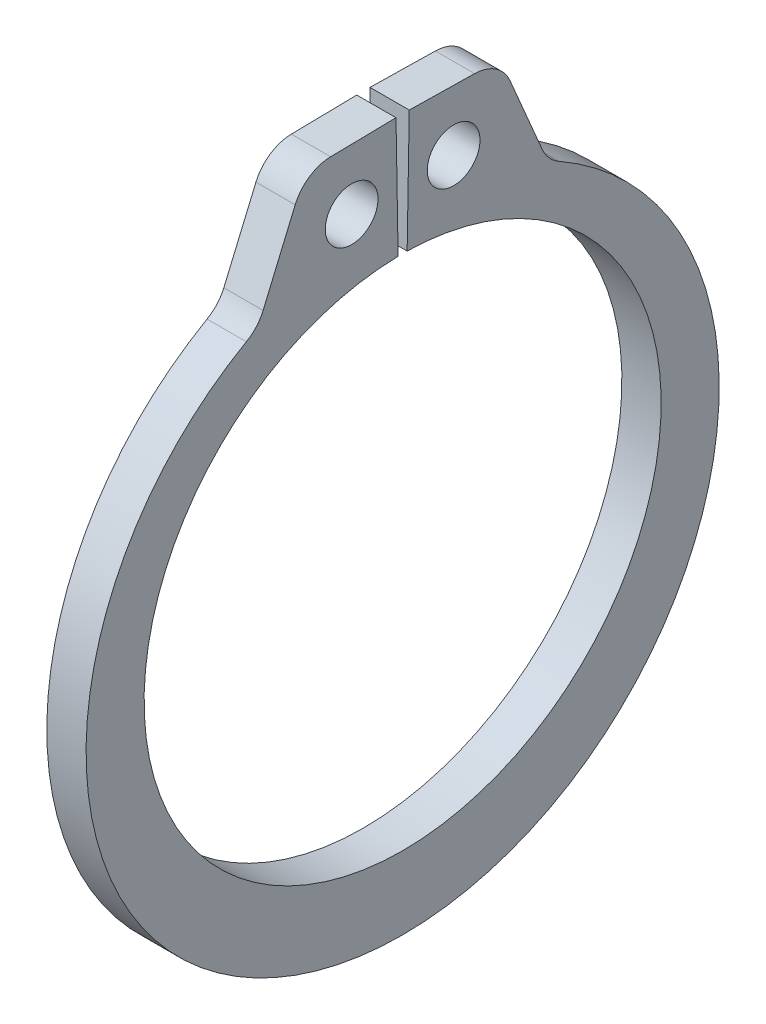
SolidWorks part; units mm, degrees
material "Cast Carbon Steel"
ref_plane "Front" through (0, 0, 0) normal (0, 0, 1) x (1, 0, 0)
ref_plane "Top" through (0, 0, 0) normal (0, 1, 0) x (1, 0, 0)
ref_plane "Right" through (0, 0, 0) normal (1, 0, 0) x (0, 0, -1)
sketch "Sketch1" plane through (0, 0, 0) normal (1, 0, 0) x (0, 0, -1)
  line L0 (0, 0) -> (0, 5.8547) construction
  line L1 (-0.1022, 5.8538) -> (-0.1501, 8.5966)
  line L2 (0.1501, 8.5966) -> (2.2071, 8.5607)
  line L3 (2.2071, 8.5607) -> (3.2813, 6.0365)
  line L4 (0.1022, 5.8538) -> (0.1501, 8.5966)
  line L5 (-0.1501, 8.5966) -> (-2.2071, 8.5607)
  line L6 (-2.2071, 8.5607) -> (-3.2813, 6.0365)
  line L7 (-3.2813, 6.0365) -> (-2.7961, 5.1439) construction
  line L8 (3.2813, 6.0365) -> (2.7961, 5.1439) construction
  line L9 (0, -5.8547) -> (0, -7.5057) construction
  line L10 (-2.2071, 8.5607) -> (-0.1022, 5.8538) construction
  line L11 (0, 5.8547) -> (0, 8.5979) construction
  line L12 (-5.8547, 0) -> (5.8547, 0) construction
  circle A0 centre (0, 0) radius 5.8547 construction
  arc A1 (-0.1022, 5.8538) -> (0.1022, 5.8538) centre (0, 0) ccw
  circle A3 centre (0, 0) radius 9.779 construction
  circle A4 centre (-1.1547, 7.2072) radius 0.5969
  circle A5 centre (1.1547, 7.2072) radius 0.5969
  arc A6 (-3.2813, 6.0365) -> (3.2813, 6.0365) centre (0, -0.3371) ccw
  point P0 (0, -7.5057)
  dimension "A" = 11.7094
  dimension "Hole" = 1.1938
  dimension "Smin" = 1.016
  dimension "H" = 2.7432
  dimension "D2" = 2.0574
  dimension "Angle" = 1
extrude "Extrude1" add sketch "Sketch1" along normal mid plane 0.889
fillet "Fillet1" radius 0.889 4 edges at (0, 6.0365, 3.2813) (0, 6.0365, -3.2813) (0, 8.5607, 2.2071) (0, 8.5607, -2.2071)
equation "\"D2@Sketch1\" = \"H@Sketch1\"*.75"
equation "\"D1@Fillet1\" = \"D1@Extrude1\""
